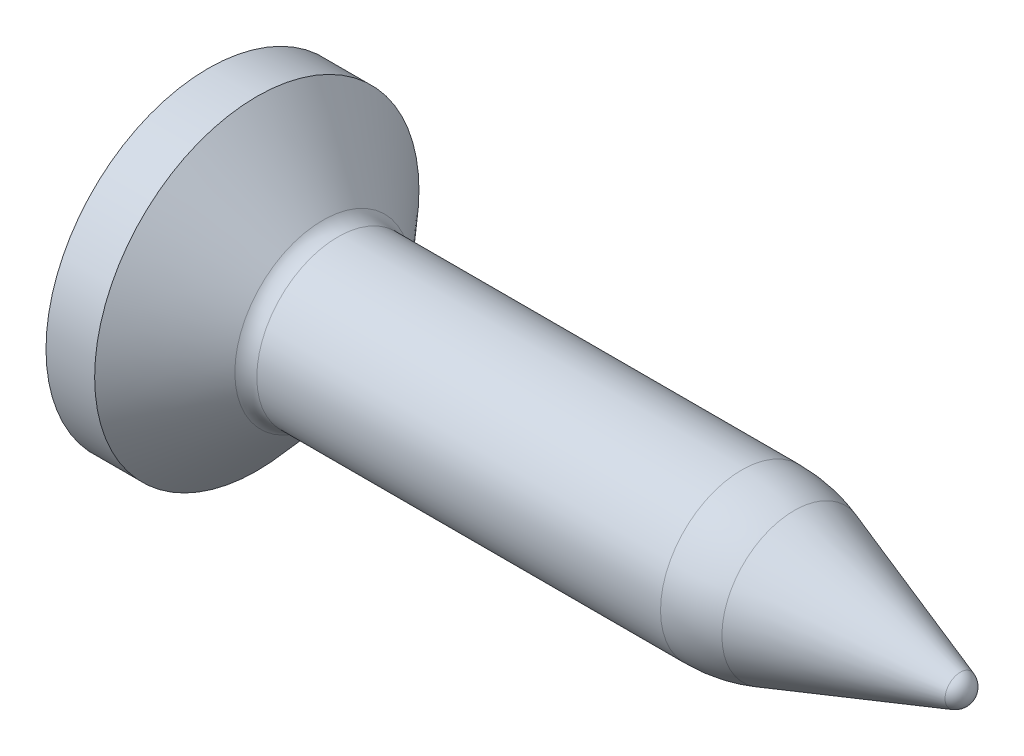
SolidWorks part; units mm, degrees
ref_plane "Front" through (0, 0, 0) normal (0, 0, 1) x (1, 0, 0)
ref_plane "Top" through (0, 0, 0) normal (0, 1, 0) x (1, 0, 0)
ref_plane "Right" through (0, 0, 0) normal (1, 0, 0) x (0, 0, -1)
sketch "Sketch1" plane through (0, 0, 0) normal (0, 0, 1) x (1, 0, 0)
  line L0 (0, 0) -> (0, 2)
  line L1 (0, 2) -> (0.6, 2)
  line L2 (0.6, 2) -> (1.413, 1.084)
  line L3 (1.6, 1) -> (6.5797, 1)
  line L6 (9.413, 0) -> (0, 0)
  line L7 (-3.9747, 0) -> (0, 0) construction
  line L8 (9.2779, 0.1892) -> (7.2283, 0.8919)
  arc A0 (1.413, 1.084) -> (1.6, 1) centre (1.6, 1.25) ccw
  arc A2 (9.2779, 0.1892) -> (9.413, 0) centre (9.213, 0) cw
  arc A3 (6.5797, 1) -> (7.2283, 0.8919) centre (6.5797, -1) cw
  point P13 (6.913, 1)
  dimension "D3" = 0.25
  dimension "D1" = 0.2
  dimension "D8" = 2
  dimension "D2" = 2
  dimension "D4" = 1.6
  dimension "D5" = 0.6
  dimension "D6" = 2.5
  dimension "D7" = 8
  dimension "D9" = 4
revolve "Revolve1" add sketch "Sketch1" angle 360 about L7
sketch "Sketch2" plane through (0, 0, 0) normal (-1, 0, 0) x (0, 0, 1)
  line L0 (1, 0) -> (0, 0) construction
  line L1 (0, 0) -> (0, 1) construction
  line L2 (-0.25, 1) -> (0.25, 1)
  line L3 (0.25, 1) -> (0.3624, 0.3624)
  line L4 (0.3624, 0.3624) -> (1, 0.25)
  line L5 (1, 0.25) -> (1, -0.25)
  line L6 (-0.25, 1) -> (-0.3624, 0.3624)
  line L7 (-0.3624, 0.3624) -> (-1, 0.25)
  line L8 (-1, 0.25) -> (-1, -0.25)
  line L9 (-0.3624, -0.3624) -> (-1, -0.25)
  line L10 (-0.25, -1) -> (-0.3624, -0.3624)
  line L11 (-0.25, -1) -> (0.25, -1)
  line L12 (0.25, -1) -> (0.3624, -0.3624)
  line L13 (0.3624, -0.3624) -> (1, -0.25)
  point P12 (-1, 0)
  dimension "D1" = 100
  dimension "D2" = 2
  dimension "D3" = 0.5
extrude "Cut-Extrude1" cut sketch "Sketch2" against normal blind 0.5
